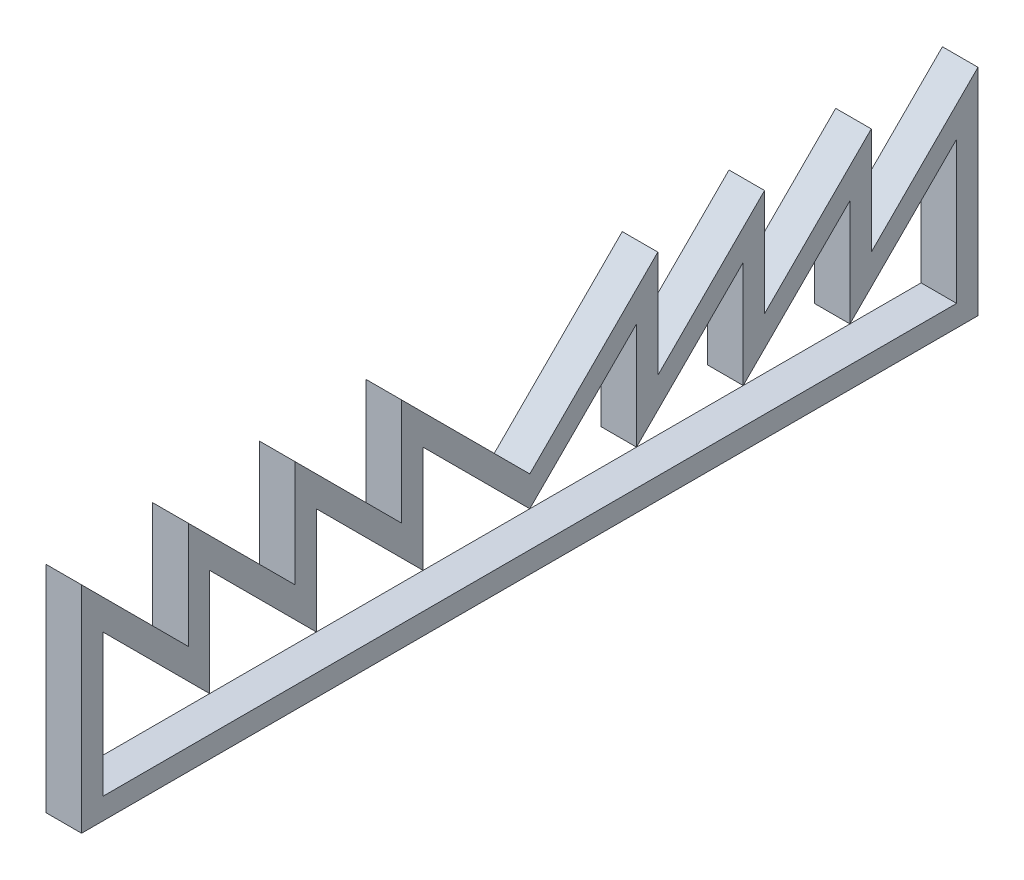
SolidWorks part; units mm, degrees
ref_plane "Front Plane" through (0, 0, 0) normal (0, 0, 1) x (1, 0, 0)
ref_plane "Top Plane" through (0, 0, 0) normal (0, 1, 0) x (1, 0, 0)
ref_plane "Right Plane" through (0, 0, 0) normal (1, 0, 0) x (0, 0, -1)
sketch "Sketch1" plane through (0, 0, 0) normal (1, 0, 0) x (0, 0, -1)
  line L0 (38.1, 12.7) -> (38.1, 50.8)
  line L1 (38.1, 50.8) -> (0, 12.7)
  line L2 (76.2, 50.8) -> (38.1, 12.7)
  line L3 (76.2, 12.7) -> (76.2, 50.8)
  line L4 (114.3, 50.8) -> (76.2, 12.7)
  line L5 (114.3, 12.7) -> (114.3, 50.8)
  line L6 (152.4, 50.8) -> (114.3, 12.7)
  line L7 (152.4, 0) -> (152.4, 50.8)
  line L8 (152.4, 0) -> (-152.4, 0)
  line L9 (0, 0) -> (0, 82.6373) construction
  line L10 (-152.4, 0) -> (-152.4, 50.8)
  line L11 (-152.4, 50.8) -> (-114.3, 12.7)
  line L12 (-114.3, 12.7) -> (-114.3, 50.8)
  line L13 (-114.3, 50.8) -> (-76.2, 12.7)
  line L14 (-76.2, 12.7) -> (-76.2, 50.8)
  line L15 (-76.2, 50.8) -> (-38.1, 12.7)
  line L16 (-38.1, 50.8) -> (0, 12.7)
  line L17 (-38.1, 12.7) -> (-38.1, 50.8)
  line L18 (-160.02, -7.62) -> (-160.02, 69.1963)
  line L19 (-160.02, 69.1963) -> (-121.92, 31.0963)
  line L20 (-121.92, 31.0963) -> (-121.92, 69.1963)
  line L21 (-121.92, 69.1963) -> (-83.82, 31.0963)
  line L22 (-83.82, 31.0963) -> (-83.82, 69.1963)
  line L23 (-83.82, 69.1963) -> (-45.72, 31.0963)
  line L24 (-45.72, 31.0963) -> (-45.72, 69.1963)
  line L25 (-45.72, 69.1963) -> (0, 23.4763)
  line L26 (45.72, 69.1963) -> (0, 23.4763)
  line L27 (45.72, 31.0963) -> (45.72, 69.1963)
  line L28 (83.82, 69.1963) -> (45.72, 31.0963)
  line L29 (83.82, 31.0963) -> (83.82, 69.1963)
  line L30 (121.92, 69.1963) -> (83.82, 31.0963)
  line L31 (121.92, 31.0963) -> (121.92, 69.1963)
  line L32 (160.02, 69.1963) -> (121.92, 31.0963)
  line L33 (160.02, -7.62) -> (160.02, 69.1963)
  line L34 (160.02, -7.62) -> (-160.02, -7.62)
  dimension "D1" = 12.7
  dimension "D2" = 38.1
  dimension "D3" = 45
  dimension "D5" = 7.62
  dimension "D4" = 4
extrude "Boss-Extrude1" add sketch "Sketch1" along normal blind 12.7
